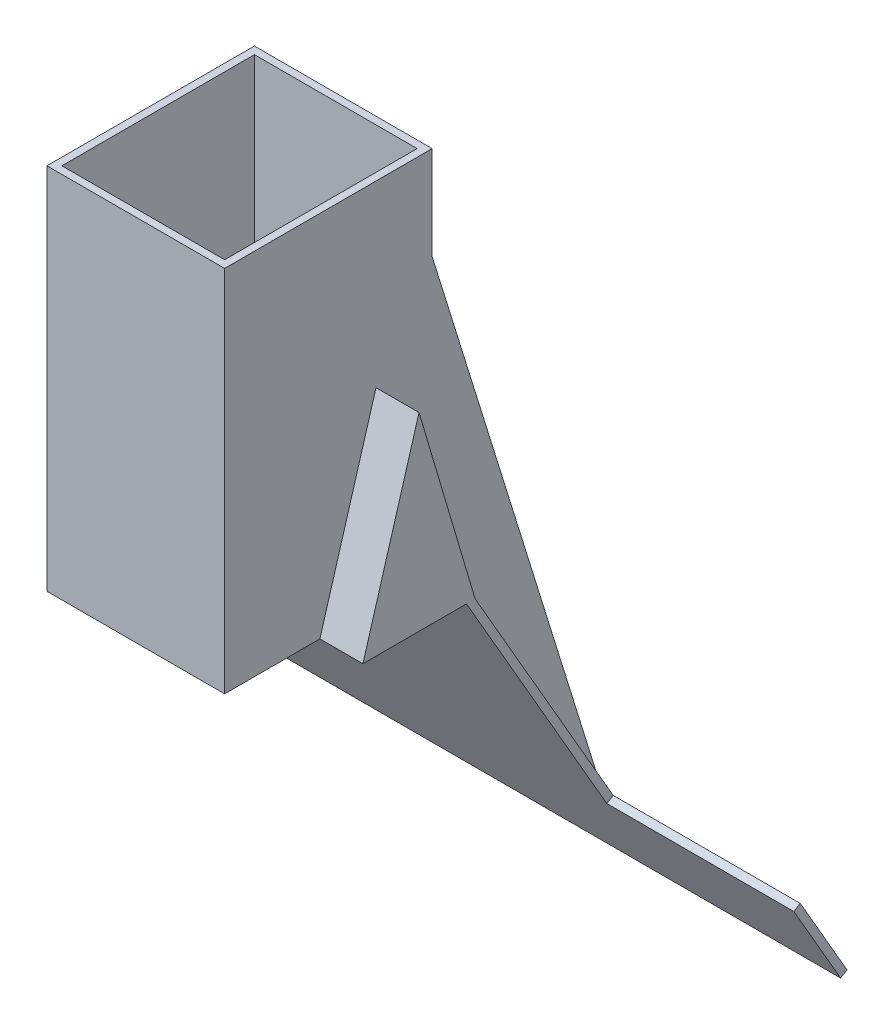
SolidWorks part; units mm, degrees
ref_plane "Ebene vorne" through (0, 0, 0) normal (0, 0, 1) x (1, 0, 0)
ref_plane "Ebene oben" through (0, 0, 0) normal (0, 1, 0) x (1, 0, 0)
ref_plane "Ebene rechts" through (0, 0, 0) normal (1, 0, 0) x (0, 0, -1)
sketch "Skizze1" plane through (0, 0, 0) normal (0, 1, 0) x (1, 0, 0)
  line L0 (0.4, 0.4) -> (0.4, 5.1)
  line L1 (0, 0) -> (9.5, 0)
  line L2 (0, 0) -> (0, 11.093)
  line L3 (0, 11.093) -> (9.5, 11.093)
  line L4 (9.5, 0) -> (9.5, 11.093)
  line L9 (0.4, 10.693) -> (9.1, 10.693)
  line L10 (9.1, 0.4) -> (9.1, 5.1)
  line L11 (0.4, 0.4) -> (9.1, 0.4)
  line L12 (0.4, 5.1) -> (9.1, 5.1)
  line L13 (9.1, 5.5) -> (0.4, 5.5)
  line L14 (0.4, 5.5) -> (0.4, 10.693)
  line L15 (0.4, 0.4) -> (0.4, 10.693) construction
  line L16 (9.1, 5.5) -> (9.1, 10.693)
  line L17 (9.1, 0.4) -> (9.1, 10.693) construction
  dimension "D1" = 11.093
  dimension "D2" = 9.5
  dimension "D3" = 0.4
  dimension "D4" = 0.4
  dimension "D5" = 5.193
extrude "Aufsatz-Linear austragen1" add sketch "Skizze1" along normal blind 19.7
sketch "Skizze2" plane through (0, 0, 0) normal (-1, 0, 0) x (0, 0, 1)
  line L1 (-11.093, 19.7) -> (-11.093, 0) construction
  line L2 (-11.093, 0) -> (-8.093, 10.13)
  line L3 (-8.093, 10.13) -> (-5.093, 0)
  line L5 (-11.093, 0) -> (0, 0) construction
  line L6 (-5.093, 0) -> (-11.093, 0)
  dimension "D1" = 10.13
  dimension "D2" = 6
  dimension "D3" = 3
extrude "Aufsatz-Linear austragen2" add sketch "Skizze2" along normal blind 2.3
ref_plane "Ebene1" through (4.75, 0, 0) normal (1, 0, 0) x (0, 0, -1)
mirror "Spiegeln1" about plane through (4.75, 0, 0) normal (1, 0, 0) of "Aufsatz-Linear austragen2"
sketch "Skizze3" plane through (-2.3, 0, 0) normal (-1, 0, 0) x (0, 0, 1)
  line L0 (-10.3797, 1) -> (-5.8063, 1)
  line L1 (-11.093, 0) -> (-5.093, 0) construction
  line L10 (-10.5574, 0.4) -> (-5.6286, 0.4)
  line L11 (-5.6286, 0.4) -> (-8.093, 8.7213)
  line L12 (-8.093, 8.7213) -> (-10.5574, 0.4)
  line L14 (-5.8063, 1) -> (-8.093, 8.7213)
  line L15 (-8.093, 8.7213) -> (-10.3797, 1)
  dimension "D1" = 0.4
  dimension "D2" = 1
extrude "Schnitt-Linear austragen1" cut sketch "Skizze3" against normal blind 13.7
sketch "Skizze4" plane through (0, 0, 0) normal (0, -1, 0) x (1, 0, 0)
  line L0 (9.1, -10.693) -> (0.4, -10.693) construction
  line L1 (-1.9, -5.5) -> (11.4, -5.5)
  line L2 (-1.9, -5.5) -> (-1.9, -10.693)
  line L3 (-1.9, -10.693) -> (11.4, -10.693)
  line L4 (11.4, -5.5) -> (11.4, -10.693)
  line L5 (0.4, -5.5) -> (9.1, -5.5) construction
  line L6 (-2.3, -11.093) -> (-2.3, -5.093) construction
  line L7 (11.8, -11.093) -> (11.8, -5.093) construction
  dimension "D1" = 0.4
  dimension "D2" = 0.4
extrude "Schnitt-Linear austragen2" cut sketch "Skizze4" against normal blind 0.4
sketch "Skizze5" plane through (-2.3, 0, 0) normal (-1, 0, 0) x (0, 0, 1)
  line L1 (-20.9775, -17.1205) -> (-20.6311, -17.3205)
  line L2 (-20.6311, -17.3205) -> (-10.6311, 0)
  line L3 (-11.093, 0) -> (-5.093, 0) construction
  line L4 (-10.6311, 0) -> (-11.093, 0)
  line L8 (-20.9775, -17.1205) -> (-11.093, 0)
  line L9 (-11.093, 19.7) -> (-11.093, 0) construction
  dimension "D1" = 150
  dimension "D2" = 20
  dimension "D4" = 0.4
extrude "Aufsatz-Linear austragen3" add sketch "Skizze5" against normal up to vertex (14.1 mm away) up to point (11.8, 0, -11.093)
sketch "Skizze6" plane through (0, 0, 0) normal (-1, 0, 0) x (0, 0, 1)
  line L0 (-20.9775, -17.1205) -> (-11.093, 0)
  line L2 (-11.093, 0) -> (-11.093, 14.7)
  line L3 (-11.093, 14.7) -> (-20.9775, -17.1205)
  dimension "D1" = 5
extrude "Aufsatz-Linear austragen4" add sketch "Skizze6" against normal up to vertex
sketch "Skizze7" plane through (0, 19.7, 0) normal (0, 1, 0) x (1, 0, 0)
  line L1 (0.4, 5.1) -> (9.1, 5.1)
  line L2 (0.4, 5.1) -> (0.4, 5.5)
  line L3 (0.4, 5.5) -> (9.1, 5.5)
  line L4 (9.1, 5.1) -> (9.1, 5.5)
extrude "Schnitt-Linear austragen3" cut sketch "Skizze7" against normal up to next
sketch "Skizze8" plane through (0, 4.6034, -7.9733) normal (0, -0.5, 0.866) x (1, 0, 0)
  line L1 (-2.3, -25.3156) -> (-12.3, -25.3156)
  line L2 (-2.3, -25.3156) -> (-2.3, -20.3156)
  line L3 (-2.3, -20.3156) -> (-12.3, -20.3156)
  line L4 (-12.3, -25.3156) -> (-12.3, -20.3156)
  line L5 (11.8, -25.3156) -> (21.8, -25.3156)
  line L6 (11.8, -25.3156) -> (11.8, -20.3156)
  line L7 (11.8, -20.3156) -> (21.8, -20.3156)
  line L8 (21.8, -25.3156) -> (21.8, -20.3156)
  dimension "D1" = 5
  dimension "D2" = 10
  dimension "D3" = 10
extrude "Aufsatz-Linear austragen5" add sketch "Skizze8" against normal up to vertex (0.4 mm away)
